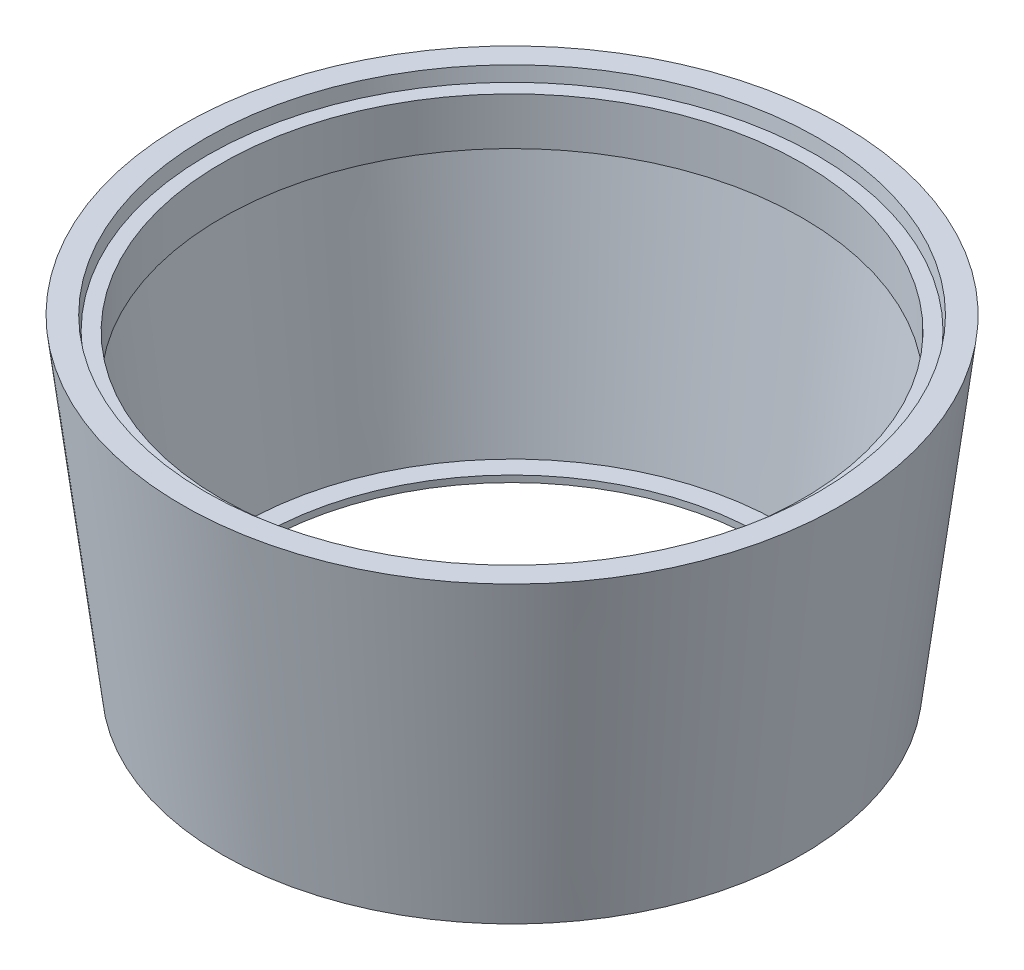
SolidWorks part; units mm, degrees
ref_plane "前视基准面" through (0, 0, 0) normal (0, 0, 1) x (1, 0, 0)
ref_plane "上视基准面" through (0, 0, 0) normal (0, 1, 0) x (1, 0, 0)
ref_plane "右视基准面" through (0, 0, 0) normal (1, 0, 0) x (0, 0, -1)
sketch "草图1" plane through (0, 0, 0) normal (0, 0, 1) x (1, 0, 0)
  line L0 (-217.1349, 0) -> (-133.2602, 0)
  line L1 (-217.1349, 0) -> (-217.1349, 14)
  line L2 (-133.2602, 0) -> (-48.8048, 687.8345)
  line L3 (-48.8048, 687.8345) -> (-98.098, 687.8345)
  line L4 (-98.098, 687.8345) -> (-101.7541, 658.0581)
  line L5 (-101.7541, 658.0581) -> (-131.9774, 658.0581)
  line L6 (-131.9774, 658.0581) -> (-131.9774, 557.0282)
  line L7 (-108.8296, 557.0282) -> (-175.5051, 14)
  line L8 (-131.9774, 557.0282) -> (-108.8296, 557.0282)
  line L9 (-217.1349, 14) -> (-175.5051, 14)
  line L10 (-217.1349, 0) -> (-752, 0) construction
  line L11 (-752, 0) -> (-752, 109.4948) construction
  point P3 (0, 0)
revolve "旋转1" add sketch "草图1" angle 360 about L11
